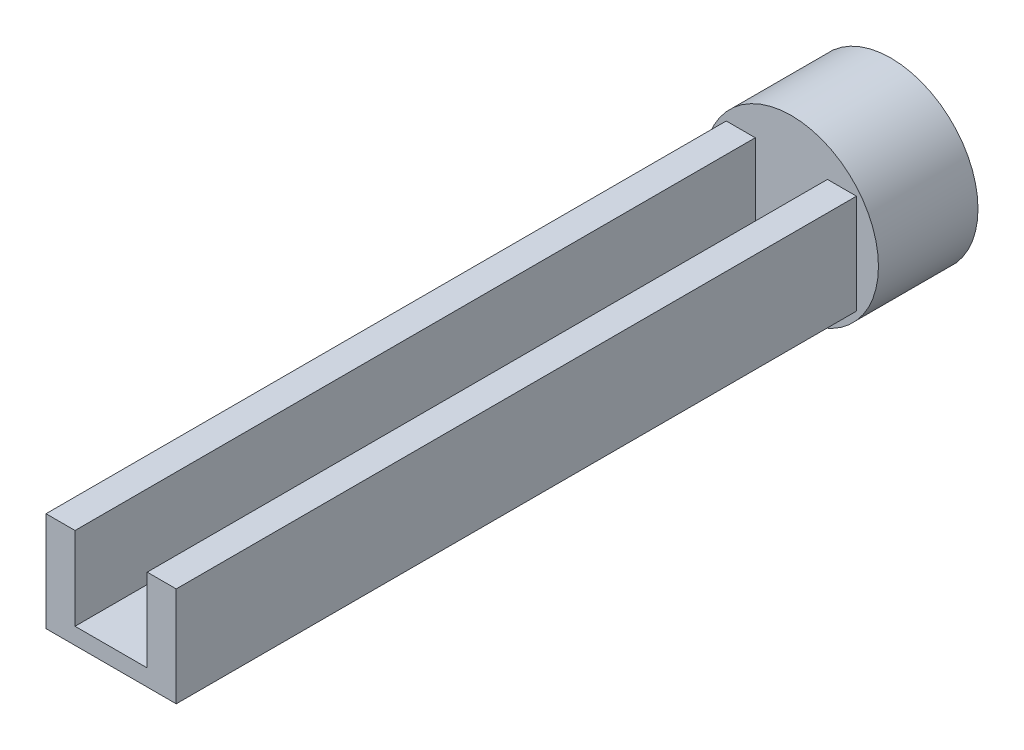
SolidWorks part; units mm, degrees
material "ABS PC"
ref_plane "Front Plane" through (0, 0, 0) normal (0, 0, 1) x (1, 0, 0)
ref_plane "Top Plane" through (0, 0, 0) normal (0, 1, 0) x (1, 0, 0)
ref_plane "Right Plane" through (0, 0, 0) normal (1, 0, 0) x (0, 0, -1)
sketch "Sketch2" plane through (0, 0, 0) normal (0, 1, 0) x (1, 0, 0)
  line L1 (7.85, -41) -> (-7.85, -41)
  line L2 (7.85, -41) -> (7.85, 41)
  line L3 (7.85, 41) -> (-7.85, 41)
  line L4 (-7.85, -41) -> (-7.85, 41)
  line L5 (7.85, -41) -> (-7.85, 41) construction
  line L6 (7.85, 41) -> (-7.85, -41) construction
  point P0 (0, 0)
  dimension "D1" = 82
  dimension "13.7" = 15.7
extrude "Boss-Extrude1" add sketch "Sketch2" along normal blind 12
sketch "Sketch3" plane through (0, 12, 0) normal (0, 1, 0) x (1, 0, 0)
  line L0 (-4.35, 41) -> (-4.35, -41)
  line L1 (7.85, 41) -> (-7.85, 41) construction
  line L2 (-7.85, -41) -> (7.85, -41) construction
  line L3 (-4.35, -41) -> (4.35, -41)
  line L4 (4.35, -41) -> (4.35, 41)
  line L5 (4.35, 41) -> (-4.35, 41)
  line L6 (-7.85, 41) -> (-7.85, -41) construction
  line L7 (7.85, -41) -> (7.85, 41) construction
  dimension "D1" = 3.5
  dimension "D2" = 3.5
extrude "Cut-Extrude1" cut sketch "Sketch3" against normal blind 10
sketch "Sketch4" plane through (0, 0, -41) normal (0, 0, -1) x (-1, 0, 0)
  line L0 (0, 0) -> (0, 17.6975) construction
  line L1 (-7.85, 12) -> (7.85, 0) construction
  line L3 (10.5, -4.5) -> (-10.5, -4.5)
  line L4 (10.5, -4.5) -> (10.5, 16.5)
  line L5 (10.5, 16.5) -> (-10.5, 16.5)
  line L6 (-10.5, -4.5) -> (-10.5, 16.5)
  line L7 (10.5, -4.5) -> (-10.5, 16.5) construction
  line L8 (10.5, 16.5) -> (-10.5, -4.5) construction
  circle A0 centre (0, 6) radius 10.5
  point P7 (0, 6)
  dimension "D1" = 21
  dimension "26.5" = 21
extrude "Boss-Extrude2" add sketch "Sketch4" along normal blind 12 contours A0
